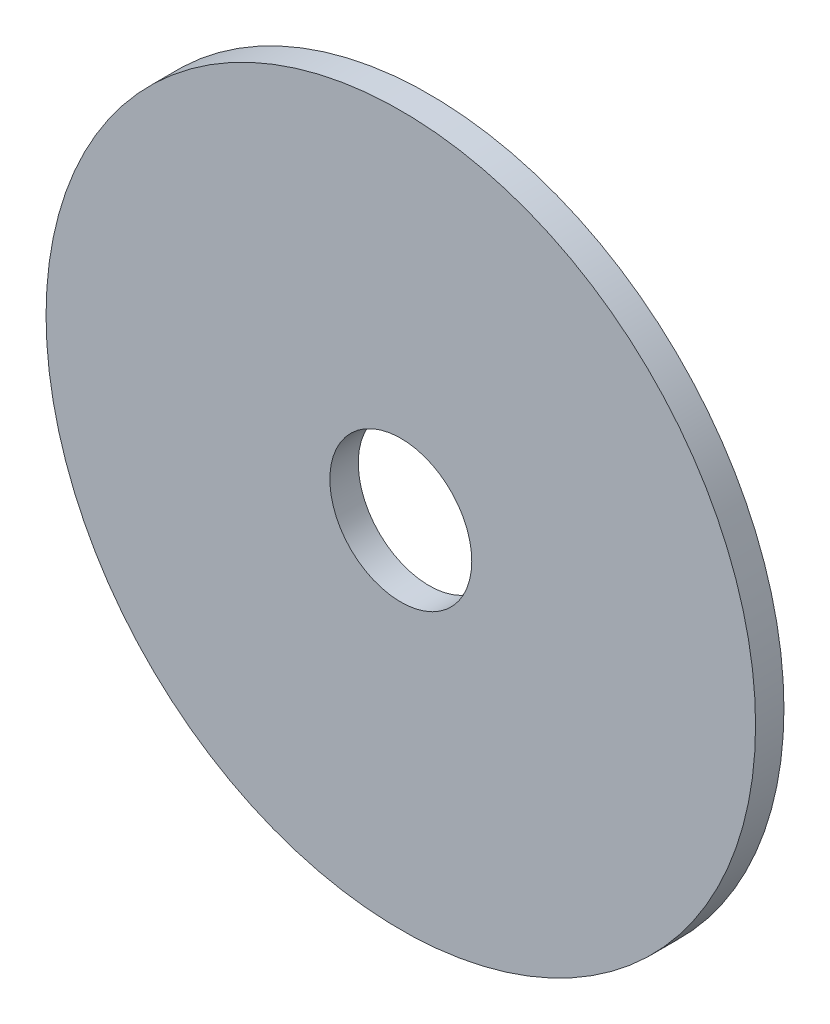
SolidWorks part; units mm, degrees
ref_plane "Front Plane" through (0, 0, 0) normal (0, 0, 1) x (1, 0, 0)
ref_plane "Top Plane" through (0, 0, 0) normal (0, 1, 0) x (1, 0, 0)
ref_plane "Right Plane" through (0, 0, 0) normal (1, 0, 0) x (0, 0, -1)
sketch "Sketch1" plane through (0, 0, 0) normal (0, 0, 1) x (1, 0, 0)
  circle A0 centre (0, 0) radius 1.5875
  circle A1 centre (0, 0) radius 7.9375
  dimension "D1" = 6.35
  dimension "D2" = 3.175
extrude "Boss-Extrude1" add sketch "Sketch1" along normal blind 0.635
